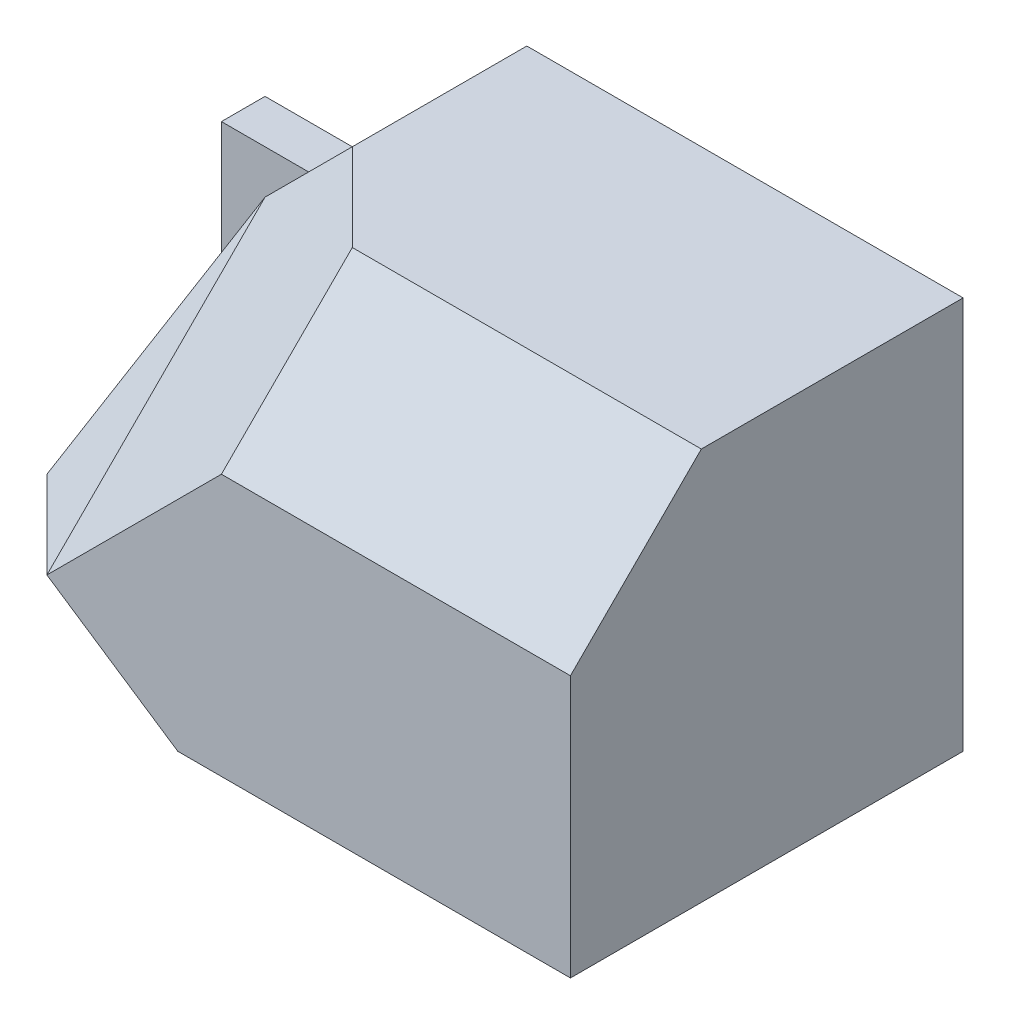
SolidWorks part; units mm, degrees
ref_plane "Front" through (0, 0, 0) normal (0, 0, 1) x (1, 0, 0)
ref_plane "Top" through (0, 0, 0) normal (0, 1, 0) x (1, 0, 0)
ref_plane "Right" through (0, 0, 0) normal (1, 0, 0) x (0, 0, -1)
sketch "Sketch1" plane through (0, 0, 0) normal (0, 0, 1) x (1, 0, 0)
  line L0 (-8, 0.5) -> (-6, 0.5)
  line L1 (-8, -4.5) -> (8, -4.5)
  line L2 (-8, -4.5) -> (-8, 4.5)
  line L3 (-8, 4.5) -> (8, 4.5)
  line L4 (8, -4.5) -> (8, 4.5)
  line L5 (-8, -4.5) -> (8, 4.5) construction
  line L6 (-8, 4.5) -> (8, -4.5) construction
  line L7 (-6, 0.5) -> (-2, 4.5)
  point P0 (0, 0)
  dimension "D1" = 16
  dimension "D2" = 9
  dimension "D3" = 2
  dimension "D4" = 4
  dimension "D5" = 4
extrude "Boss-Extrude1" add sketch "Sketch1" along normal blind 9 contours L7 L0 L2 L1 L4 L3
sketch "Sketch2" plane through (0, 0, 9) normal (0, 0, 1) x (1, 0, 0)
  line L0 (-8, 0.5) -> (-6, 0.5)
  line L1 (-6, 0.5) -> (-8, -4.5)
  line L2 (-8, -4.5) -> (-8, 0.5)
extrude "Cut-Extrude1" cut sketch "Sketch2" against normal blind 8
sketch3d "3DSketch1"
  line L0 (-6, 0.5, 9) -> (-6, 0.5, 1) construction
  line L1 (-8, -4.5, 5) -> (-6, 0.5, 2)
  line L2 (-8, -4.5, 9) -> (-8, -4.5, 1) construction
  line L3 (-6, 0.5, 2) -> (-4, 2.5, 2)
  line L4 (-6, 0.5, 0) -> (-2, 4.5, 0) construction
  line L5 (-4, 2.5, 2) -> (-4, -2.5, 7)
  line L6 (-4, -2.5, 7) -> (-6, -4.5, 7)
  line L7 (-8, -4.5, 5) -> (-6, -4.5, 7)
  point P0 (-6, 0.5, 2)
  point P1 (-4, 2.5, 2)
  dimension "D1" = 2
  dimension "D2" = 2
  dimension "D3" = 7
  dimension "D4" = 2
  dimension "D5" = 2
  dimension "D7" = 0
  dimension "D6" = 5
  dimension "D8" = 2
extrude "Cut-Extrude2" cut sketch "3DSketch1" along direction (0, 0, 1) on the side against the normal blind 8
sketch3d "3DSketch2"
  line L0 (-4, 2.5, 2) -> (-4, 2.5, 9) construction
  line L1 (-4, -2.5, 9) -> (-4, 2.5, 4)
  line L2 (-4, -2.5, 9) -> (0, 1.5, 9)
  line L4 (0, 1.5, 9) -> (0, 4.5, 6)
  line L5 (-4, 2.5, 4) -> (-2, 4.5, 4)
  line L6 (-2, 4.5, 9) -> (-2, 4.5, 0) construction
  line L7 (-2, 4.5, 4) -> (0, 4.5, 6)
  point P0 (-4, 2.5, 4)
  dimension "D1" = 9
  dimension "D2" = 3
  dimension "D3" = 2
  dimension "D4" = 8
  dimension "D5" = 8
  dimension "D6" = 0
  dimension "D7" = 6
  dimension "D8" = 4
extrude "Cut-Extrude3" cut sketch "3DSketch2" along direction (0, 0, 1) on the side against the normal blind 8
sketch "Sketch3" plane through (0, 0, 0) normal (-1, 0, 0) x (0, 0, 1)
  line L0 (9, 1.5) -> (6, 4.5)
  line L1 (6, 4.5) -> (9, 4.5)
  line L2 (9, 4.5) -> (9, 1.5)
extrude "Cut-Extrude4" cut sketch "Sketch3" against normal blind 8
sketch "Sketch4" plane through (0, 0, 9) normal (0, 0, 1) x (1, 0, 0)
  line L0 (-4, -2.5) -> (-1, -4.5)
  line L1 (-6, -4.5) -> (8, -4.5) construction
  line L2 (-1, -4.5) -> (-6, -4.5)
  line L3 (-6, -4.5) -> (-4, -2.5)
  dimension "D1" = 3
extrude "Cut-Extrude5" cut sketch "Sketch4" against normal blind 2
